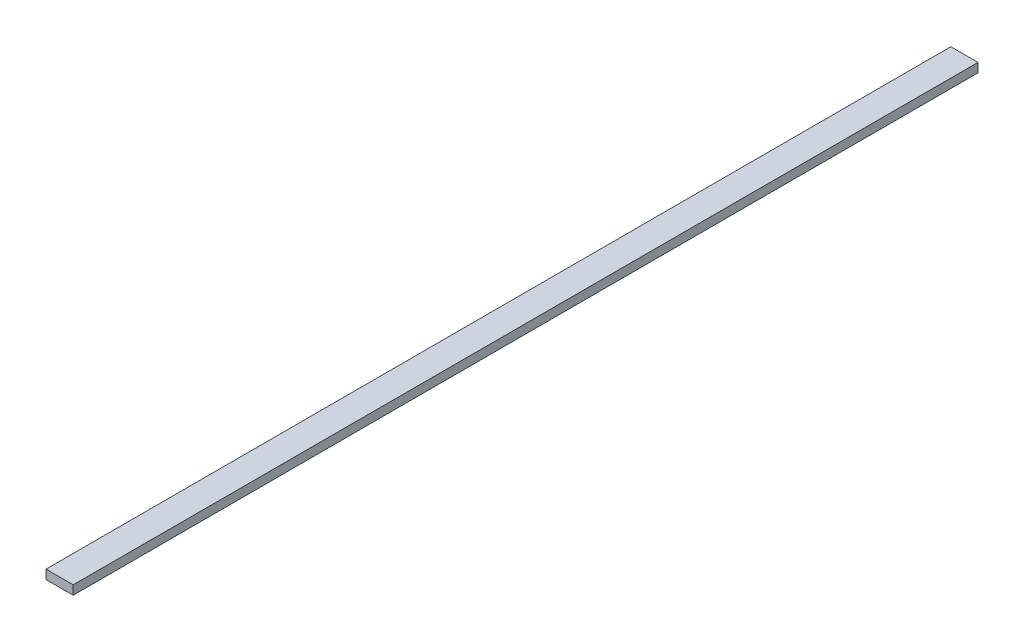
SolidWorks part; units mm, degrees
ref_plane "Front Plane" through (0, 0, 0) normal (0, 0, 1) x (1, 0, 0)
ref_plane "Top Plane" through (0, 0, 0) normal (0, 1, 0) x (1, 0, 0)
ref_plane "Right Plane" through (0, 0, 0) normal (1, 0, 0) x (0, 0, -1)
sketch "Sketch1" plane through (0, 0, 0) normal (0, 1, 0) x (1, 0, 0)
  line L0 (-150, 5000) -> (150, -5000) construction
  line L1 (-150, 5000) -> (150, 5000)
  line L2 (-150, 5000) -> (-150, -5000)
  line L3 (-150, -5000) -> (150, -5000)
  line L4 (150, 5000) -> (150, -5000)
  dimension "D1" = 300
  dimension "D2" = 10000
extrude "Boss-Extrude1" add sketch "Sketch1" along normal blind 100
